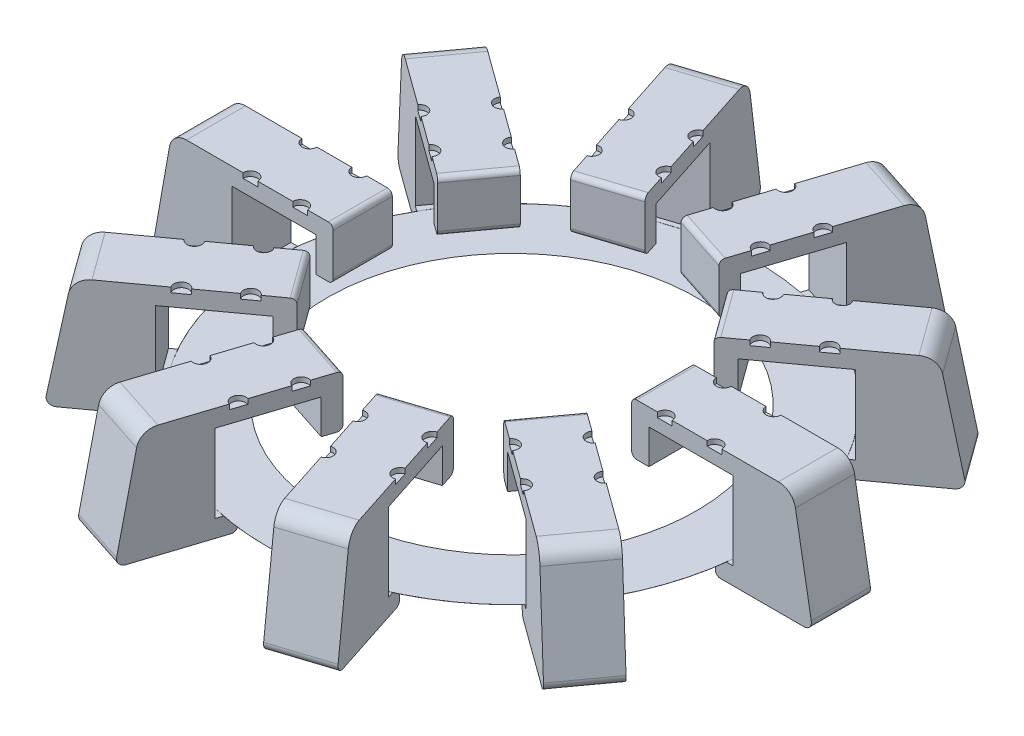
SolidWorks part; units mm, degrees
material "Cast Carbon Steel"
ref_plane "Front Plane" through (0, 0, 0) normal (0, 0, 1) x (1, 0, 0)
ref_plane "Top Plane" through (0, 0, 0) normal (0, 1, 0) x (1, 0, 0)
ref_plane "Right Plane" through (0, 0, 0) normal (1, 0, 0) x (0, 0, -1)
sketch "Sketch1" plane through (0, 0, 0) normal (0, 0, 1) x (1, 0, 0)
  line L0 (-33.8, 8.9) -> (-31.3, 8.9)
  line L1 (-49.89, 15.4) -> (-34.5, 15.4) construction
  line L2 (-49.89, 15.4) -> (-49.89, 0.5) construction
  line L3 (-49.89, 0.5) -> (-34.5, 0.5) construction
  line L4 (-34.5, 15.4) -> (-34.5, 0.5) construction
  line L5 (-30.3, 9.9) -> (-30.3, 18.4)
  line L6 (-31.3, 19.4) -> (-60.1129, 19.4)
  line L7 (-63.5597, 16.5078) -> (-66.7772, -1.7395)
  line L8 (-65.3, -3.5) -> (-48.29, -3.5)
  line L9 (-47.29, -2.5) -> (-47.29, 0)
  line L10 (-47.29, 0) -> (-50.89, 0)
  line L11 (-50.89, 0) -> (-50.89, 15.9)
  line L12 (-50.89, 15.9) -> (-33.8, 15.9)
  line L13 (-33.8, 15.9) -> (-33.8, 8.9)
  line L14 (-47.29, 0) -> (0, 0) construction
  arc A0 (-66.7772, -1.7395) -> (-65.3, -3.5) centre (-65.3, -2) ccw
  arc A1 (-60.1129, 19.4) -> (-63.5597, 16.5078) centre (-60.1129, 15.9) ccw
  arc A2 (-48.29, -3.5) -> (-47.29, -2.5) centre (-48.29, -2.5) ccw
  arc A3 (-31.3, 8.9) -> (-30.3, 9.9) centre (-31.3, 9.9) ccw
  arc A4 (-30.3, 18.4) -> (-31.3, 19.4) centre (-31.3, 18.4) ccw
  point P15 (-42.345, 15.9)
  point P23 (-47.29, -3.5)
  point P26 (-30.3, 8.9)
  dimension "D11" = 1.5
  dimension "D12" = 3.5
  dimension "D13" = 1
  dimension "D1" = 15.39
  dimension "D2" = 14.9
  dimension "D3" = 3.5
  dimension "D4" = 3.5
  dimension "D5" = 3.5
  dimension "D6" = 0.5
  dimension "D7" = 0.5
  dimension "D8" = 1
  dimension "D9" = 0.7
  dimension "D10" = 80
  dimension "D14" = 35
  dimension "D15" = 3.6
  dimension "D16" = 7
  dimension "D17" = 49.89
extrude "Boss-Extrude1" add sketch "Sketch1" along normal mid plane 12
sketch "Sketch4" plane through (0, 19.4, 0) normal (0, 1, 0) x (1, 0, 0)
  line L0 (-31.3, -6) -> (-60.1129, -6) construction
  line L1 (-31.3, 6) -> (-60.1129, 6) construction
  circle A0 centre (0, 0) radius 37.5 construction
  circle A1 centre (0, 0) radius 47.5 construction
  circle A2 centre (-37.0169, 6) radius 1.5
  circle A3 centre (-37.0169, -6) radius 1.5
  circle A4 centre (-47.1195, 6) radius 1.5
  circle A5 centre (-47.1195, -6) radius 1.5
  dimension "D1" = 75
  dimension "D2" = 95
  dimension "D3" = 3
extrude "Cut-Extrude1" cut sketch "Sketch4" against normal blind 1
sketch "Sketch5" plane through (0, 0, 0) normal (0, 1, 0) x (1, 0, 0)
  circle A0 centre (0, 0) radius 49.89
  circle A1 centre (0, 0) radius 37.5
  dimension "D1" = 99.78
  dimension "D2" = 75
sketch "Sketch6" plane through (0, 0, 0) normal (1, 0, 0) x (0, 0, -1)
  line L0 (0, 12.6742) -> (0, -29.7092) construction
extrude "Boss-Extrude2" add sketch "Sketch5" along normal blind 0.0001
pattern_circular "CirPattern2" count 10 over 360 about axis through (0, 0, 0) along (0, 1, 0) of "Boss-Extrude1", "Cut-Extrude1"
